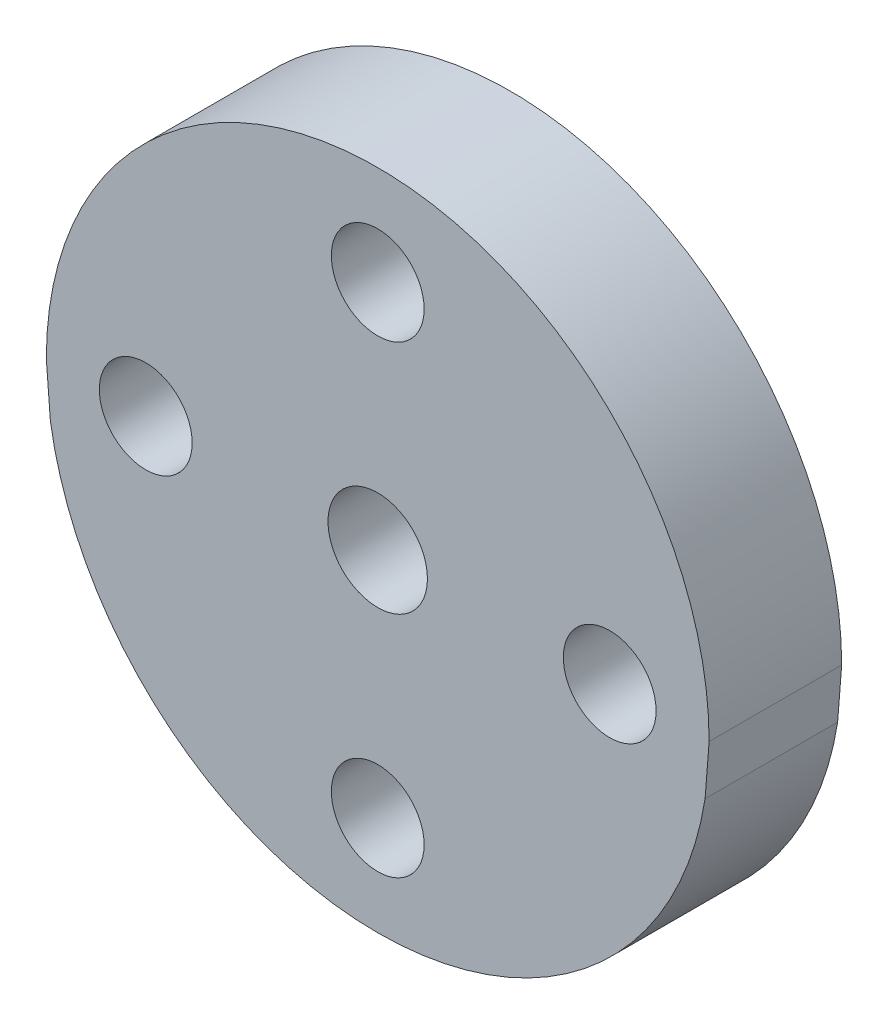
SolidWorks part; units mm, degrees
ref_plane "Front Plane" through (0, 0, 0) normal (0, 0, 1) x (1, 0, 0)
ref_plane "Top Plane" through (0, 0, 0) normal (0, 1, 0) x (1, 0, 0)
ref_plane "Right Plane" through (0, 0, 0) normal (1, 0, 0) x (0, 0, -1)
sketch "Sketch1" plane through (0, 0, 0) normal (0, 0, 1) x (1, 0, 0)
  line L0 (-10, 0) -> (-7.6529, -30)
  line L1 (10, 0) -> (7.6529, -30)
  line L2 (0, 5.6) -> (0, 1.5)
  arc A0 (10, 0) -> (-10, 0) centre (0, 0) ccw
  circle A2 centre (0, 0) radius 1.5
  circle A4 centre (7, 0) radius 1.4
  circle A5 centre (0, -7) radius 1.4
  circle A6 centre (-7, 0) radius 1.4
  circle A7 centre (0, 7) radius 1.4
  circle A8 centre (0, -30) radius 1.4
  arc A9 (-7.6529, -30) -> (7.6529, -30) centre (0, -30) ccw
  point P18 (0, 0)
  dimension "D1" = 20
  dimension "D3" = 3
  dimension "D6" = 2.8
  dimension "D10" = 2.8
  dimension "D7" = 7
  dimension "D9" = 4.1
  dimension "D11" = 30
  dimension "D8" = 4
extrude "Boss-Extrude1" add sketch "Sketch1" along normal blind 4 contours A6 | A7 | A2 | A4 | A5 | A8 | A9 L1 A0 L0
sketch "Sketch2" plane through (0, 0, 4) normal (0, 0, 1) x (1, 0, 0)
  line L0 (-10, 0) -> (-16.5881, -36.3718)
  line L1 (-16.5881, -36.3718) -> (1.2507, -40.3213)
  line L2 (1.2507, -40.3213) -> (12.8812, -32.9073)
  line L3 (12.8812, -32.9073) -> (10, 0)
  circle A0 centre (0, 0) radius 10
  line M4 (-10, 0) -> (-7.6529, -30)
  arc M5 (-7.6529, -30) -> (7.6529, -30) centre (0, -30) ccw
  line M6 (7.6529, -30) -> (10, 0)
  circle M10 centre (0, -30) radius 1.4
extrude "Cut-Extrude1" cut sketch "Sketch2" against normal blind 10 contours A0 M4 M5 M6 M10
